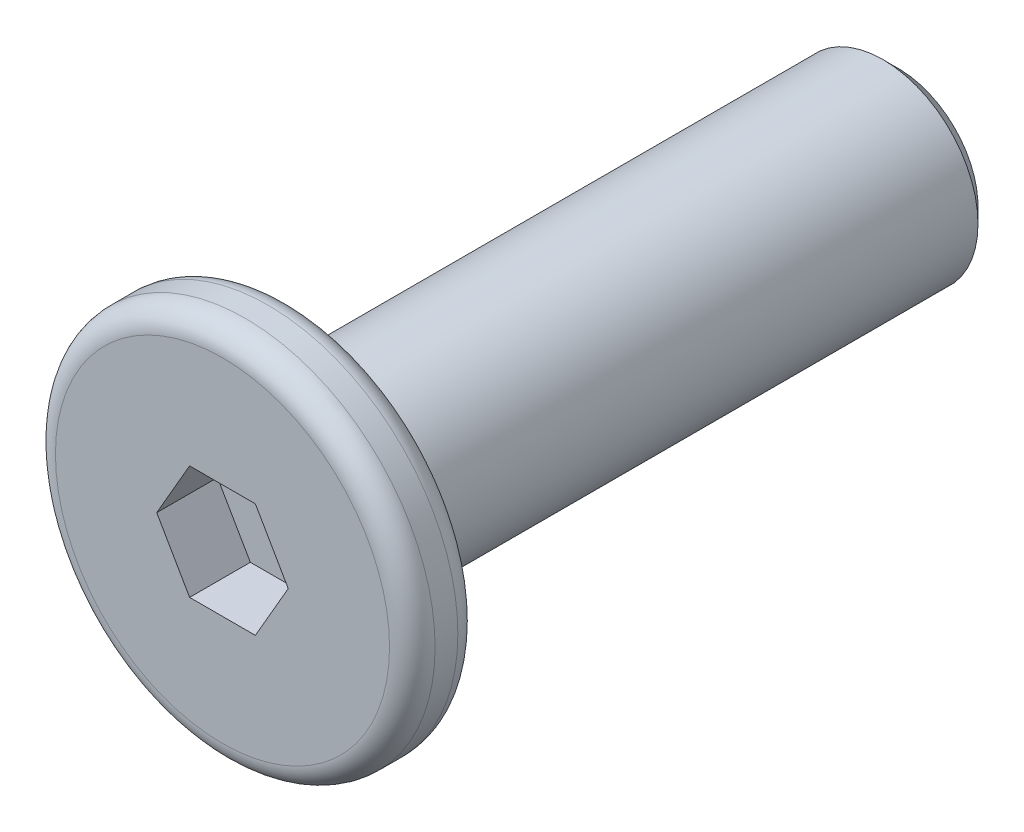
SolidWorks part; units mm, degrees
ref_plane "前视基准面" through (0, 0, 0) normal (0, 0, 1) x (1, 0, 0)
ref_plane "上视基准面" through (0, 0, 0) normal (0, 1, 0) x (1, 0, 0)
ref_plane "右视基准面" through (0, 0, 0) normal (1, 0, 0) x (0, 0, -1)
sketch "草图1" plane through (0, 0, 0) normal (0, 0, 1) x (1, 0, 0)
  circle A0 centre (0, 0) radius 2.5
  dimension "D1" = 5
extrude "凸台-拉伸1" add sketch "草图1" along normal mid plane 0.9
sketch "草图2" plane through (0, 0, -0.45) normal (0, 0, -1) x (-1, 0, 0)
  circle A0 centre (0, 0) radius 1.25
  dimension "D1" = 2.5
extrude "凸台-拉伸2" add sketch "草图2" along normal blind 8
chamfer "倒角1" distance 0.2 angle 45 1 edges at (-1.25, 0, -8.45)
sketch "草图3" plane through (0, 0, 0.45) normal (0, 0, 1) x (1, 0, 0)
  line L1 (0.866, 0) -> (0.433, 0.75)
  line L2 (0.433, 0.75) -> (-0.433, 0.75)
  line L3 (-0.433, 0.75) -> (-0.866, 0)
  line L4 (-0.866, 0) -> (-0.433, -0.75)
  line L5 (-0.433, -0.75) -> (0.433, -0.75)
  line L6 (0.433, -0.75) -> (0.866, 0)
  circle A0 centre (0, 0) radius 0.75 construction
  dimension "D1" = 1.5
extrude "切除-拉伸1" cut sketch "草图3" against normal blind 0.8
fillet "圆角2" radius 0.3 2 edges at (2.5, 0, -0.45) (2.5, 0, 0.45)
